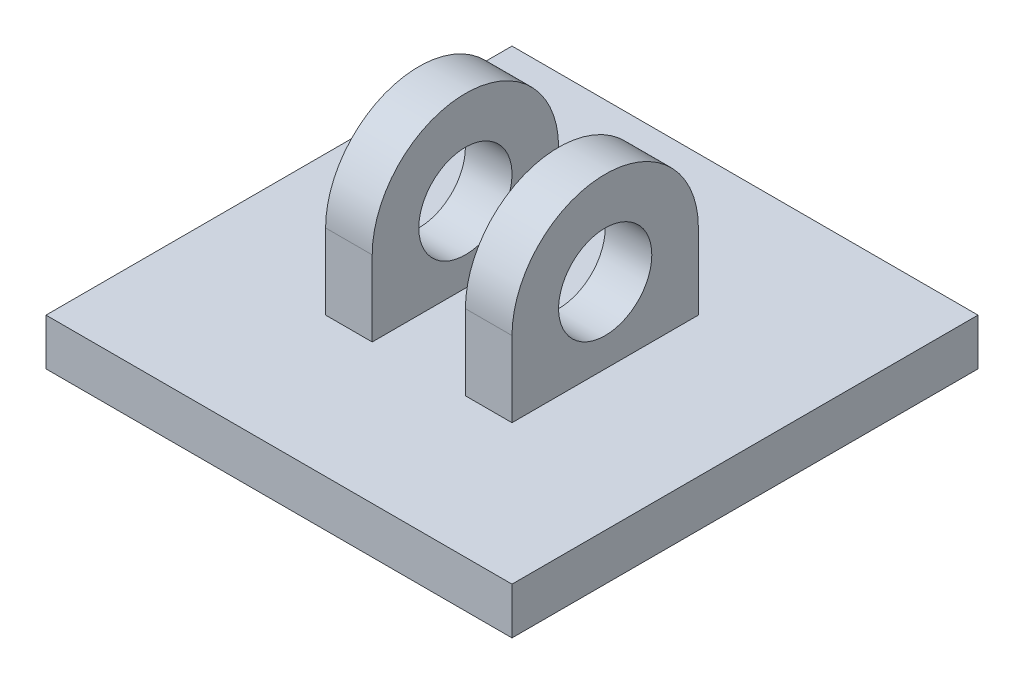
SolidWorks part; units mm, degrees
material "Brass"
ref_plane "Front Plane" through (0, 0, 0) normal (0, 0, 1) x (1, 0, 0)
ref_plane "Top Plane" through (0, 0, 0) normal (0, 1, 0) x (1, 0, 0)
ref_plane "Right Plane" through (0, 0, 0) normal (1, 0, 0) x (0, 0, -1)
sketch "Sketch1" plane through (0, 0, 0) normal (0, 0, 1) x (1, 0, 0)
  line L0 (27.5, 0) -> (-27.5, 0) construction
  line L1 (-25, 0) -> (25, 0)
  line L2 (-25, 0) -> (-25, 5)
  line L3 (-25, 5) -> (25, 5)
  line L4 (25, 0) -> (25, 5)
  line L5 (0, -2.75) -> (0, 2.75) construction
  dimension "D1" = 50
  dimension "D2" = 25
  dimension "D3" = 5
extrude "Boss-Extrude1" add sketch "Sketch1" against normal blind 50
ref_plane "Plane1" through (5, 0, 0) normal (1, 0, 0) x (0, 0, -1)
sketch "Sketch2" plane through (5, 0, 0) normal (1, 0, 0) x (0, 0, -1)
  line L0 (50, 5) -> (0, 5) construction
  line L1 (15, 5) -> (35, 5)
  line L2 (15, 5) -> (15, 13.0977)
  line L4 (35, 5) -> (35, 13.0977)
  line L5 (0, 12.7037) -> (0, -12.7037) construction
  arc A0 (35, 13.0977) -> (15, 13.0977) centre (25, 13.0977) ccw
  dimension "D1" = 20
  dimension "D2" = 15
extrude "Boss-Extrude2" add sketch "Sketch2" along normal blind 5
sketch "Sketch3" plane through (10, 0, 0) normal (1, 0, 0) x (0, 0, -1)
  circle A0 centre (25, 13.0977) radius 5
  arc A1 (35, 13.0977) -> (15, 13.0977) centre (25, 13.0977) ccw construction
  dimension "D1" = 10
extrude "Cut-Extrude1" cut sketch "Sketch3" against normal through all
mirror "Mirror1" about plane through (0, 0, 0) normal (1, 0, 0) of "Cut-Extrude1", "Boss-Extrude2"
